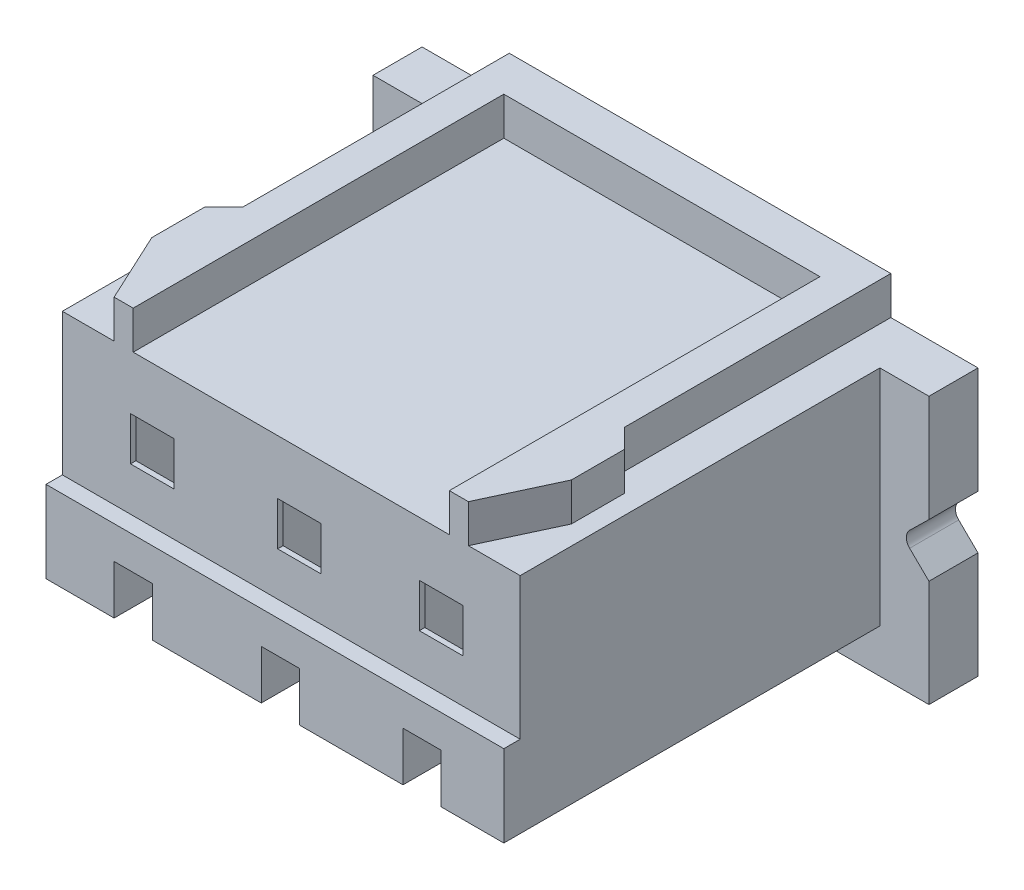
SolidWorks part; units mm, degrees
ref_plane "Plan de face" through (0, 0, 0) normal (0, 0, 1) x (1, 0, 0)
ref_plane "Plan de dessus" through (0, 0, 0) normal (0, 1, 0) x (1, 0, 0)
ref_plane "Plan de droite" through (0, 0, 0) normal (1, 0, 0) x (0, 0, -1)
sketch "Esquisse1" plane through (0, 0, 0) normal (0, 0, 1) x (1, 0, 0)
  line L1 (-5.1, 2.8) -> (5.1, 2.8)
  line L2 (-5.1, 2.8) -> (-5.1, -2.8)
  line L3 (-5.1, -2.8) -> (5.1, -2.8)
  line L4 (5.1, 2.8) -> (5.1, -2.8)
  line L5 (-5.1, 2.8) -> (5.1, -2.8) construction
  line L6 (-5.1, -2.8) -> (5.1, 2.8) construction
  point P0 (0, 0)
  dimension "D1" = 10.2
  dimension "D2" = 5.6
extrude "Boss.-Extru.1" add sketch "Esquisse1" against normal blind 7.8
sketch "Esquisse2" plane through (0, 0, 0) normal (0, 0, 1) x (1, 0, 0)
  line L0 (5.1, -2.8) -> (5.1, 2.8) construction
  line L1 (-5.1, 2.8) -> (5.1, 2.8)
  line L2 (-5.1, 2.8) -> (-5.1, -0.5)
  line L3 (-5.1, -0.5) -> (5.1, -0.5)
  line L4 (5.1, 2.8) -> (5.1, -0.5)
  dimension "D1" = 3.3
extrude "Enlèv. mat.-Extru.1" cut sketch "Esquisse2" against normal blind 0.3
sketch "Esquisse4" plane through (0, 0, 0) normal (0, 0, 1) x (1, 0, 0)
  line L0 (5.1, 2.8) -> (-5.1, 2.8) construction
  line L1 (-5.1, -2.8) -> (5.1, -2.8) construction
  line L2 (5.1, 2.8) -> (-5.1, 2.8)
  line L3 (-5.1, -2.8) -> (5.1, -2.8)
  line L4 (-4.2, 2.8) -> (-4.2, -2)
  line L5 (-4.2, -2) -> (4.2, -2)
  line L6 (4.2, -2) -> (4.2, 2.8)
  line L7 (-5.1, 2.8) -> (-5.1, -0.5) construction
  line L8 (5.1, -0.5) -> (5.1, 2.8) construction
  line L9 (-5.1, -0.5) -> (-5.1, -2.8) construction
  line L10 (5.1, -2.8) -> (5.1, -0.5) construction
  line L11 (-5.1, 2.8) -> (-5.1, -0.5)
  line L12 (-5.1, -0.5) -> (-5.1, -2.8)
  line L13 (5.1, -2.8) -> (5.1, -0.5)
  line L14 (5.1, -0.5) -> (5.1, 2.8)
  line M1 (5.1, -0.5) -> (-5.1, -0.5)
  line M2 (-5.1, -0.5) -> (-5.1, -2.8)
  line M3 (-5.1, -2.8) -> (5.1, -2.8)
  line M4 (5.1, -2.8) -> (5.1, -0.5)
  dimension "D1" = 0.9
  dimension "D2" = 0.9
  dimension "D3" = 0.8
extrude "Enlèv. mat.-Extru.2" cut sketch "Esquisse4" against normal blind 6.9 contours L2 L11 L4 M1 | L6 L5 L4 M1 M2 M3 M4 | L14 L2 L6 M1
sketch "Esquisse5" plane through (0, 2.8, 0) normal (0, 1, 0) x (1, 0, 0)
  line L0 (-3.5, 7.8) -> (-3.5, 2.91)
  line L1 (-3.5, 2.91) -> (-3.85, 2.56)
  line L2 (-3.85, 2.56) -> (-3.85, 1.59)
  line L3 (-3.85, 1.59) -> (-3.25, 0.3)
  line L4 (4.2, 0.3) -> (-4.2, 0.3) construction
  line L5 (-2.9, 0.3) -> (-2.9, 7.1)
  line L6 (-2.9, 7.1) -> (2.9, 7.1)
  line L7 (0, 7.8) -> (0, 0.3) construction
  line L8 (-5.1, 6.9) -> (-4.2, 6.9)
  line L9 (-4.2, 6.9) -> (-4.2, 0.3)
  line L10 (-4.2, 0.3) -> (4.2, 0.3)
  line L11 (4.2, 0.3) -> (4.2, 6.9)
  line L12 (4.2, 6.9) -> (5.1, 6.9)
  line L13 (5.1, 6.9) -> (5.1, 7.8)
  line L14 (5.1, 7.8) -> (-5.1, 7.8)
  line L15 (-5.1, 7.8) -> (-5.1, 6.9)
  line L16 (-5.1, 6.9) -> (-4.2, 6.9)
  line L17 (-4.2, 6.9) -> (-4.2, 0.3)
  line L18 (-4.2, 0.3) -> (4.2, 0.3)
  line L19 (4.2, 0.3) -> (4.2, 6.9)
  line L20 (4.2, 6.9) -> (5.1, 6.9)
  line L21 (5.1, 6.9) -> (5.1, 7.8)
  line L22 (5.1, 7.8) -> (-5.1, 7.8)
  line L23 (-5.1, 7.8) -> (-5.1, 6.9)
  line L24 (5.1, 7.8) -> (5.1, 6.9)
  line L25 (4.2, 6.9) -> (4.2, 0.3)
  line L26 (5.1, 6.9) -> (4.2, 6.9)
  line L27 (2.9, 0.3) -> (2.9, 7.1)
  line L28 (3.85, 1.59) -> (3.25, 0.3)
  line L29 (3.85, 2.56) -> (3.85, 1.59)
  line L30 (3.5, 2.91) -> (3.85, 2.56)
  line L31 (3.5, 7.8) -> (3.5, 2.91)
  point P21 (0, 7.1)
  line M9 (-5.1, 6.9) -> (-4.2, 6.9)
  line M10 (-4.2, 6.9) -> (-4.2, 0.3)
  line M11 (-4.2, 0.3) -> (4.2, 0.3)
  line M12 (4.2, 0.3) -> (4.2, 6.9)
  line M13 (4.2, 6.9) -> (5.1, 6.9)
  line M14 (5.1, 6.9) -> (5.1, 7.8)
  line M15 (5.1, 7.8) -> (-5.1, 7.8)
  line M16 (-5.1, 7.8) -> (-5.1, 6.9)
  dimension "D2" = 0.35
  dimension "D3" = 0.7
  dimension "D4" = 1.29
  dimension "D5" = 0.6
  dimension "D6" = 0.35
  dimension "D7" = 0.97
  dimension "D8" = 0.6
  dimension "D9" = 0.7
  dimension "D1" = 0
extrude "Enlèv. mat.-Extru.3" cut sketch "Esquisse5" against normal blind 0.7 contours L7 L6 L5 M11 | L6 L7 L18 L27 | L31 L30 L29 L28 M15 M11 M12 M13 M14 | L3 L2 L1 L0 M15 M16 M9 M10 M11
sketch "Esquisse6" plane through (0, 0, 0) normal (0, 0, 1) x (1, 0, 0)
  line L0 (-2.95, -2) -> (-2.95, -1.1)
  line L1 (-4.2, -2) -> (4.2, -2) construction
  line L2 (-2.95, -1.1) -> (-2.25, -1.1)
  line L3 (-2.25, -1.1) -> (-2.25, -2)
  line L4 (-4.2, -0.5) -> (-4.2, -2) construction
  line L5 (-0.25, -2) -> (-0.25, -1.1)
  line L6 (-0.25, -1.1) -> (0.45, -1.1)
  line L7 (0.45, -1.1) -> (0.45, -2)
  line L9 (2.35, -2) -> (2.35, -1.1)
  line L10 (2.35, -1.1) -> (3.05, -1.1)
  line L11 (3.05, -1.1) -> (3.05, -2)
  line L13 (-2.95, -2) -> (-2.25, -2)
  line L14 (-0.25, -2) -> (0.45, -2)
  line L15 (2.35, -2) -> (3.05, -2)
  dimension "D1" = 1.25
  dimension "D2" = 0.9
  dimension "D3" = 0.7
  dimension "D4" = 2
  dimension "D5" = 1.9
  dimension "D6" = 0.7
  dimension "D7" = 0.7
extrude "Enlèv. mat.-Extru.4" cut sketch "Esquisse6" against normal blind 3
sketch "Esquisse7" plane through (0, 0, -0.3) normal (0, 0, 1) x (1, 0, 0)
  line L0 (-2.9, 2.1) -> (2.9, 2.1) construction
  line L1 (-2.95, 1.1) -> (-2.15, 1.1)
  line L2 (-2.95, 1.1) -> (-2.95, 0.3)
  line L3 (-2.95, 0.3) -> (-2.15, 0.3)
  line L4 (-2.15, 1.1) -> (-2.15, 0.3)
  line L5 (-0.25, 1.1) -> (0.55, 1.1)
  line L6 (-0.25, 1.1) -> (-0.25, 0.3)
  line L7 (-0.25, 0.3) -> (0.55, 0.3)
  line L8 (0.55, 1.1) -> (0.55, 0.3)
  line L9 (2.35, 1.1) -> (3.15, 1.1)
  line L10 (2.35, 1.1) -> (2.35, 0.3)
  line L11 (2.35, 0.3) -> (3.15, 0.3)
  line L12 (3.15, 1.1) -> (3.15, 0.3)
  line L13 (-2.95, -1.1) -> (-2.95, -2) construction
  line L14 (-0.25, -1.1) -> (-0.25, -2) construction
  line L15 (2.35, -1.1) -> (2.35, -2) construction
  dimension "D1" = 0.8
  dimension "D2" = 1
extrude "Enlèv. mat.-Extru.5" cut sketch "Esquisse7" against normal blind 0.5
sketch "Esquisse8" plane through (0, 0, -7.8) normal (0, 0, -1) x (-1, 0, 0)
  line L0 (-0.8, 1.5) -> (-0.8, -1.5)
  line L1 (-0.8, 1.5) -> (0.8, 1.5)
  line L2 (0, 1.5) -> (0, 0) construction
  line L3 (-3.5, 2.8) -> (3.5, 2.8) construction
  line L4 (-0.8, -1.5) -> (-0.4, -1.5)
  line L5 (-0.4, -1.5) -> (-0.4, -1.7)
  line L6 (-0.4, -1.7) -> (0.4, -1.7)
  line L7 (0.4, -1.7) -> (0.4, -1.5)
  line L8 (0.4, -1.5) -> (0.8, -1.5)
  line L9 (0.8, -1.5) -> (0.8, 1.5)
  line L10 (0, 0) -> (0, -1.7) construction
  line L11 (-0.7, 0.95) -> (-0.7, -1.45)
  line L12 (-0.7, -1.45) -> (0.7, -1.45)
  line L13 (0.7, -1.45) -> (0.7, 0.95)
  line L14 (0, -1.45) -> (0, 0.95) construction
  line L15 (1.7, 1.5) -> (1.7, -1.5)
  line L16 (1.7, 1.5) -> (3.3, 1.5)
  line L17 (1.7, -1.5) -> (2.1, -1.5)
  line L18 (2.1, -1.5) -> (2.1, -1.7)
  line L19 (2.1, -1.7) -> (2.9, -1.7)
  line L20 (2.9, -1.7) -> (2.9, -1.5)
  line L21 (2.9, -1.5) -> (3.3, -1.5)
  line L22 (3.3, -1.5) -> (3.3, 1.5)
  line L23 (1.8, 0.95) -> (1.8, -1.45)
  line L24 (1.8, -1.45) -> (3.2, -1.45)
  line L25 (3.2, -1.45) -> (3.2, 0.95)
  line L26 (2.5, 1.5) -> (2.5, 0) construction
  line L27 (2.5, 0) -> (2.5, -1.7) construction
  line L28 (2.5, -1.45) -> (2.5, 0.95) construction
  line L29 (-3.3, 1.5) -> (-3.3, -1.5)
  line L30 (-3.3, 1.5) -> (-1.7, 1.5)
  line L31 (-3.3, -1.5) -> (-2.9, -1.5)
  line L32 (-2.9, -1.5) -> (-2.9, -1.7)
  line L33 (-2.9, -1.7) -> (-2.1, -1.7)
  line L34 (-2.1, -1.7) -> (-2.1, -1.5)
  line L35 (-2.1, -1.5) -> (-1.7, -1.5)
  line L36 (-1.7, -1.5) -> (-1.7, 1.5)
  line L37 (-3.2, 0.95) -> (-3.2, -1.45)
  line L38 (-3.2, -1.45) -> (-1.8, -1.45)
  line L39 (-1.8, -1.45) -> (-1.8, 0.95)
  line L40 (-2.5, 1.5) -> (-2.5, 0) construction
  line L41 (-2.5, 0) -> (-2.5, -1.7) construction
  line L42 (-2.5, -1.45) -> (-2.5, 0.95) construction
  arc A0 (-0.7, 0.95) -> (0, 0.95) centre (-0.35, 0.95) cw
  arc A1 (0, 0.95) -> (0.7, 0.95) centre (0.35, 0.95) cw
  arc A2 (1.8, 0.95) -> (2.5, 0.95) centre (2.15, 0.95) cw
  arc A3 (2.5, 0.95) -> (3.2, 0.95) centre (2.85, 0.95) cw
  arc A4 (-3.2, 0.95) -> (-2.5, 0.95) centre (-2.85, 0.95) cw
  arc A5 (-2.5, 0.95) -> (-1.8, 0.95) centre (-2.15, 0.95) cw
  dimension "D1" = 3
  dimension "D2" = 1.6
  dimension "D3" = 1.3
  dimension "D4" = 0.8
  dimension "D5" = 0.2
  dimension "D6" = 0.05
  dimension "D7" = 0.1
  dimension "D8" = 0.1
  dimension "D9" = 2.4
  dimension "D11" = 2.5
  dimension "D13" = 2.5
  dimension "D10" = 2
  dimension "D12" = 2
extrude "Enlèv. mat.-Extru.6" cut sketch "Esquisse8" against normal blind 7 contours L8 L9 L1 L0 L4 L5 L6 L7 A0 A1 L13 L12 L11 | L35 L36 L30 L29 L31 L32 L33 L34 A4 A5 L39 L38 L37 | L21 L22 L16 L15 L17 L18 L19 L20 A2 A3 L25 L24 L23
sketch "Esquisse9" plane through (0, 0, -7.8) normal (0, 0, -1) x (-1, 0, 0)
  line L0 (-0.7, 0.95) -> (-0.7, -1.45) construction
  line L1 (-0.7, -1.45) -> (0.7, -1.45) construction
  line L2 (0.7, -1.45) -> (0.7, 0.95) construction
  line L3 (-3.2, 0.95) -> (-3.2, -1.45) construction
  line L4 (-3.2, -1.45) -> (-1.8, -1.45) construction
  line L5 (-1.8, -1.45) -> (-1.8, 0.95) construction
  line L6 (1.8, 0.95) -> (1.8, -1.45) construction
  line L7 (1.8, -1.45) -> (3.2, -1.45) construction
  line L8 (3.2, -1.45) -> (3.2, 0.95) construction
  line L9 (-0.7, 0.95) -> (-0.7, -1.45)
  line L10 (-0.7, -1.45) -> (0.7, -1.45)
  line L11 (0.7, -1.45) -> (0.7, 0.95)
  line L12 (-3.2, 0.95) -> (-3.2, -1.45)
  line L13 (-3.2, -1.45) -> (-1.8, -1.45)
  line L14 (-1.8, -1.45) -> (-1.8, 0.95)
  line L15 (1.8, 0.95) -> (1.8, -1.45)
  line L16 (1.8, -1.45) -> (3.2, -1.45)
  line L17 (3.2, -1.45) -> (3.2, 0.95)
  arc A0 (0.7, 0.95) -> (0, 0.95) centre (0.35, 0.95) ccw construction
  arc A1 (0, 0.95) -> (-0.7, 0.95) centre (-0.35, 0.95) ccw construction
  arc A2 (-1.8, 0.95) -> (-2.5, 0.95) centre (-2.15, 0.95) ccw construction
  arc A3 (-2.5, 0.95) -> (-3.2, 0.95) centre (-2.85, 0.95) ccw construction
  arc A4 (3.2, 0.95) -> (2.5, 0.95) centre (2.85, 0.95) ccw construction
  arc A5 (2.5, 0.95) -> (1.8, 0.95) centre (2.15, 0.95) ccw construction
  arc A6 (0.7, 0.95) -> (0, 0.95) centre (0.35, 0.95) ccw
  arc A7 (0, 0.95) -> (-0.7, 0.95) centre (-0.35, 0.95) ccw
  arc A8 (-1.8, 0.95) -> (-2.5, 0.95) centre (-2.15, 0.95) ccw
  arc A9 (-2.5, 0.95) -> (-3.2, 0.95) centre (-2.85, 0.95) ccw
  arc A10 (3.2, 0.95) -> (2.5, 0.95) centre (2.85, 0.95) ccw
  arc A11 (2.5, 0.95) -> (1.8, 0.95) centre (2.15, 0.95) ccw
extrude "Enlèv. mat.-Extru.7" cut sketch "Esquisse9" against normal blind 0.8
sketch "Esquisse10" plane through (0, 0, -7) normal (0, 0, -1) x (-1, 0, 0)
  line L0 (0, -1.45) -> (0, 0) construction
  line L1 (-0.7, -1.45) -> (0.7, -1.45) construction
  line L2 (-2.5, 0) -> (0, 0) construction
  line L3 (0, 0) -> (2.5, 0) construction
  line L4 (-2.5, 0) -> (-2.5, -1.45) construction
  line L5 (-3.2, -1.45) -> (-1.8, -1.45) construction
  line L6 (2.5, 0) -> (2.5, -1.45) construction
  line L7 (1.8, -1.45) -> (3.2, -1.45) construction
  circle A0 centre (0, 0) radius 0.6
  circle A1 centre (-2.5, 0) radius 0.6
  circle A2 centre (2.5, 0) radius 0.6
  dimension "D2" = 1.2
  dimension "D1" = 1.45
extrude "Enlèv. mat.-Extru.8" cut sketch "Esquisse10" against normal blind 4
ref_plane "Plan1" through (0, -1.9735, 0.2288) normal (0, -0.9933, 0.1152) x (-1, 0, 0)
sketch "Sketch2" plane through (0, 0, -7.8) normal (0, 0, -1) x (-1, 0, 0)
  line L8 (3.3, -1.5) -> (3.3, 1.5)
  line L9 (3.3, -1.5) -> (3.3, 1.5)
  line L10 (2.9, -1.5) -> (3.3, -1.5)
  line L11 (2.9, -1.5) -> (3.3, -1.5)
  line L12 (2.9, -1.7) -> (2.9, -1.5)
  line L13 (2.9, -1.7) -> (2.9, -1.5)
  line L14 (2.1, -1.7) -> (2.9, -1.7)
  line L15 (2.1, -1.7) -> (2.9, -1.7)
  line L16 (2.1, -1.5) -> (2.1, -1.7)
  line L17 (2.1, -1.5) -> (2.1, -1.7)
  line L18 (1.7, -1.5) -> (2.1, -1.5)
  line L19 (1.7, -1.5) -> (2.1, -1.5)
  line L20 (1.7, 1.5) -> (1.7, -1.5)
  line L21 (1.7, 1.5) -> (1.7, -1.5)
  line L22 (3.3, 1.5) -> (1.7, 1.5)
  line L23 (3.3, 1.5) -> (1.7, 1.5)
  line L32 (0.8, -1.5) -> (0.8, 1.5)
  line L33 (0.4, -1.5) -> (0.8, -1.5)
  line L34 (0.4, -1.7) -> (0.4, -1.5)
  line L35 (-0.4, -1.7) -> (0.4, -1.7)
  line L36 (-0.4, -1.5) -> (-0.4, -1.7)
  line L37 (-0.8, -1.5) -> (-0.4, -1.5)
  line L38 (-0.8, 1.5) -> (-0.8, -1.5)
  line L39 (0.8, 1.5) -> (-0.8, 1.5)
  line L48 (-1.7, -1.5) -> (-1.7, 1.5)
  line L49 (-2.1, -1.5) -> (-1.7, -1.5)
  line L50 (-2.1, -1.7) -> (-2.1, -1.5)
  line L51 (-2.9, -1.7) -> (-2.1, -1.7)
  line L52 (-2.9, -1.5) -> (-2.9, -1.7)
  line L53 (-3.3, -1.5) -> (-2.9, -1.5)
  line L54 (-3.3, 1.5) -> (-3.3, -1.5)
  line L55 (-1.7, 1.5) -> (-3.3, 1.5)
  dimension "D1" = 0
sketch "Sketch3" plane through (0, 0, -7.8) normal (0, 0, -1) x (-1, 0, 0)
  line L0 (3.6, 1.5) -> (-3.938, 1.5) construction
  line L1 (1, 1.5) -> (1, -1.3)
  line L2 (-1.2, -1.3) -> (-1.2, 1.5)
  line L3 (-0.45, -1.3) -> (-1.2, -1.3)
  line L4 (2.85, -1.7) -> (2.85, -1.3)
  line L5 (2.85, -1.7) -> (2.15, -1.7)
  line L6 (-0.45, -1.7) -> (-0.45, -1.3)
  line L7 (0.25, -1.7) -> (0.25, -1.3)
  line L8 (2.5, -1.7) -> (2.5, 1.5) construction
  line L9 (2.1, -1.7) -> (2.9, -1.7) construction
  line L10 (3.6, 1.5) -> (1.4, 1.5)
  line L11 (1, -1.3) -> (0.25, -1.3)
  line L12 (0.25, -1.7) -> (-0.45, -1.7)
  line L13 (1, 1.5) -> (-1.2, 1.5)
  line L14 (-0.8, 1.5) -> (0.8, 1.5) construction
  line L15 (-1.6, 1.5) -> (-1.6, -1.3)
  line L16 (-3.8, -1.3) -> (-3.8, 1.5)
  line L17 (-3.05, -1.3) -> (-3.8, -1.3)
  line L18 (-3.05, -1.7) -> (-3.05, -1.3)
  line L19 (-2.35, -1.7) -> (-2.35, -1.3)
  line L20 (-1.6, -1.3) -> (-2.35, -1.3)
  line L21 (-2.35, -1.7) -> (-3.05, -1.7)
  line L22 (-1.6, 1.5) -> (-3.8, 1.5)
  line L23 (-0.4, -1.7) -> (0.4, -1.7) construction
  line L26 (1.7, 1.5) -> (3.3, 1.5) construction
  line L27 (2.15, -1.7) -> (2.15, -1.3)
  line L28 (2.15, -1.3) -> (1.4, -1.3)
  line L29 (1.4, -1.3) -> (1.4, 1.5)
  line L30 (3.6, 1.5) -> (3.6, -1.3)
  line L31 (3.6, -1.3) -> (2.85, -1.3)
  dimension "D1" = 0.7
  dimension "D2" = 2.2
  dimension "D3" = 2.8
  dimension "D4" = 0.4
  dimension "D6" = 0.4
  dimension "D5" = 3
extrude "Cut-Extrude2" cut sketch "Sketch3" against normal blind 7.4
sketch "Sketch4" plane through (0, 0, -7.8) normal (0, 0, -1) x (-1, 0, 0)
  line L0 (2.85, -1.7) -> (2.85, -1.3) construction
  line L1 (2.85, -1.7) -> (2.15, -1.7) construction
  line L2 (2.15, -1.7) -> (2.15, -1.3) construction
  line L3 (2.15, -1.3) -> (1.4, -1.3) construction
  line L4 (1.4, -1.3) -> (1.4, 1.5) construction
  line L5 (3.6, 1.5) -> (1.4, 1.5) construction
  line L6 (3.6, 1.5) -> (3.6, -1.3) construction
  line L7 (3.6, -1.3) -> (2.85, -1.3) construction
  line L8 (0.25, -1.7) -> (0.25, -1.3) construction
  line L9 (0.25, -1.7) -> (-0.45, -1.7) construction
  line L10 (-0.45, -1.7) -> (-0.45, -1.3) construction
  line L11 (-0.45, -1.3) -> (-1.2, -1.3) construction
  line L12 (-1.2, -1.3) -> (-1.2, 1.5) construction
  line L13 (1, 1.5) -> (-1.2, 1.5) construction
  line L14 (1, 1.5) -> (1, -1.3) construction
  line L15 (1, -1.3) -> (0.25, -1.3) construction
  line L16 (-1.6, -1.3) -> (-2.35, -1.3) construction
  line L17 (-1.6, 1.5) -> (-1.6, -1.3) construction
  line L18 (-1.6, 1.5) -> (-3.8, 1.5) construction
  line L19 (-3.8, -1.3) -> (-3.8, 1.5) construction
  line L20 (-3.05, -1.3) -> (-3.8, -1.3) construction
  line L21 (-3.05, -1.7) -> (-3.05, -1.3) construction
  line L22 (-2.35, -1.7) -> (-3.05, -1.7) construction
  line L23 (-2.35, -1.7) -> (-2.35, -1.3) construction
  line L24 (2.85, -1.7) -> (2.85, -1.3)
  line L25 (2.85, -1.7) -> (2.15, -1.7)
  line L26 (2.15, -1.7) -> (2.15, -1.3)
  line L27 (2.15, -1.3) -> (1.4, -1.3)
  line L28 (1.4, -1.3) -> (1.4, 1.5)
  line L29 (3.6, 1.5) -> (1.4, 1.5)
  line L30 (3.6, 1.5) -> (3.6, -1.3)
  line L31 (3.6, -1.3) -> (2.85, -1.3)
  line L32 (0.25, -1.7) -> (0.25, -1.3)
  line L33 (0.25, -1.7) -> (-0.45, -1.7)
  line L34 (-0.45, -1.7) -> (-0.45, -1.3)
  line L35 (-0.45, -1.3) -> (-1.2, -1.3)
  line L36 (-1.2, -1.3) -> (-1.2, 1.5)
  line L37 (1, 1.5) -> (-1.2, 1.5)
  line L38 (1, 1.5) -> (1, -1.3)
  line L39 (1, -1.3) -> (0.25, -1.3)
  line L40 (-1.6, -1.3) -> (-2.35, -1.3)
  line L41 (-1.6, 1.5) -> (-1.6, -1.3)
  line L42 (-1.6, 1.5) -> (-3.8, 1.5)
  line L43 (-3.8, -1.3) -> (-3.8, 1.5)
  line L44 (-3.05, -1.3) -> (-3.8, -1.3)
  line L45 (-3.05, -1.7) -> (-3.05, -1.3)
  line L46 (-2.35, -1.7) -> (-3.05, -1.7)
  line L47 (-2.35, -1.7) -> (-2.35, -1.3)
  line L48 (3.3, -1.3) -> (3.3, -1.7)
  line L49 (3.3, -1.7) -> (2.85, -1.7)
  line L50 (2.15, -1.7) -> (1.7, -1.7)
  line L51 (1.7, -1.7) -> (1.7, -1.3)
  line L52 (0.8, -1.3) -> (0.8, -1.7)
  line L53 (0.8, -1.7) -> (0.25, -1.7)
  line L54 (0.25, -1.7) -> (0.2517, -1.6946)
  line L55 (-0.8, -1.3) -> (-0.8, -1.7)
  line L56 (-0.8, -1.7) -> (-0.45, -1.7)
  line L57 (-1.7, -1.3) -> (-1.7, -1.7)
  line L58 (-1.7, -1.7) -> (-2.35, -1.7)
  line L59 (-2.35, -1.7) -> (-2.3485, -1.7022)
  line L60 (-3.3, -1.3) -> (-3.3, -1.7)
  line L61 (-3.3, -1.7) -> (-3.05, -1.7)
extrude "Boss-Extrude2" add sketch "Sketch4" against normal blind 7
sketch "Sketch5" plane through (0, -2, 0) normal (0, -1, 0) x (1, 0, 0)
  line L1 (-2.95, -0.3948) -> (-2.25, -0.3948)
  line L2 (-2.95, -0.3948) -> (-2.95, -3)
  line L3 (-2.95, -3) -> (-2.25, -3)
  line L4 (-2.25, -0.3948) -> (-2.25, -3)
  line L5 (-0.25, -0.4081) -> (0.45, -0.4081)
  line L6 (-0.25, -0.4081) -> (-0.25, -3)
  line L7 (-0.25, -3) -> (0.45, -3)
  line L8 (0.45, -0.4081) -> (0.45, -3)
  line L9 (2.35, -0.4) -> (3.05, -0.4)
  line L10 (2.35, -0.4) -> (2.35, -3)
  line L11 (2.35, -3) -> (3.05, -3)
  line L12 (3.05, -0.4) -> (3.05, -3)
  line L16 (3.05, -3) -> (3.05, 0) construction
  line L22 (-2.25, -3) -> (-2.25, 0) construction
  line L23 (0.45, -3) -> (0.45, 0) construction
extrude "Cut-Extrude3" cut sketch "Sketch5" against normal blind 2
sketch "Sketch7" plane through (0, 0, -7.8) normal (0, 0, -1) x (-1, 0, 0)
  line L0 (-5.1, 0.1399) -> (-4.6, -0.35)
  line L1 (-5.1, -2.8) -> (-5.1, 2.1) construction
  line L2 (-4.6, -0.35) -> (-5.1, -0.8399)
  line L4 (-5.1, 0.1399) -> (-5.1, -0.8399)
  point P8 (-5.6192, -0.35)
  dimension "D1" = 0.5
  dimension "D2" = 0.7
  dimension "D3" = 0.7
extrude "Cut-Extrude4" cut sketch "Sketch7" against normal blind 10
fillet "Fillet1" radius 0.2 1 edges at (4.6, -0.35, -7.35)
sketch "Sketch8" plane through (0, 0, -7.8) normal (0, 0, -1) x (-1, 0, 0)
  line L0 (-4.3553, -2.4396) -> (4.6063, -2.4396) construction
  text T0 "        1           2            3" font "Century Gothic" height 0.5
extrude "Boss-Extrude3" add sketch "Sketch8" along normal blind 0.1
